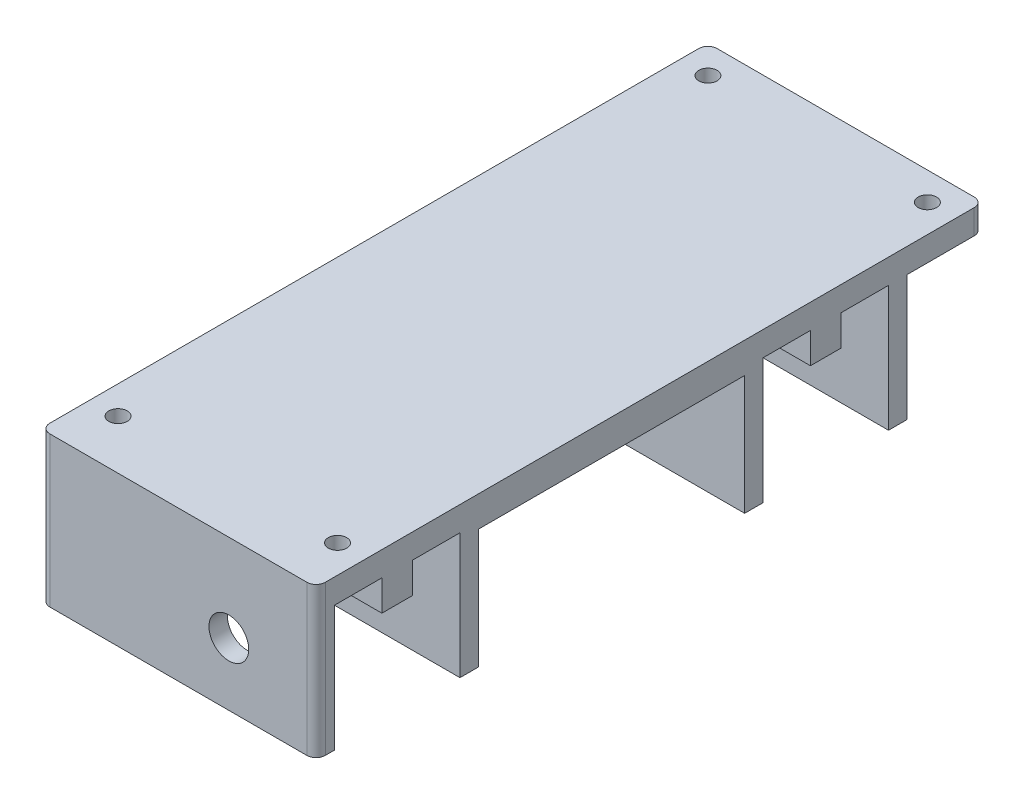
SolidWorks part; units mm, degrees
ref_plane "Front Plane" through (0, 0, 0) normal (0, 0, 1) x (1, 0, 0)
ref_plane "Top Plane" through (0, 0, 0) normal (0, 1, 0) x (1, 0, 0)
ref_plane "Right Plane" through (0, 0, 0) normal (1, 0, 0) x (0, 0, -1)
sketch "Sketch1" plane through (0, 0, 0) normal (0, 1, 0) x (1, 0, 0)
  line L1 (21, -54.5) -> (-21, -54.5)
  line L2 (22.5, -53) -> (22.5, 53)
  line L3 (21, 54.5) -> (-21, 54.5)
  line L4 (-22.5, -53) -> (-22.5, 53)
  line L5 (22.5, -54.5) -> (-22.5, 54.5) construction
  line L6 (22.5, 54.5) -> (-22.5, -54.5) construction
  circle A0 centre (17.925, -46.425) radius 1.5
  circle A1 centre (-17.925, -46.425) radius 1.5
  circle A2 centre (17.925, 49.925) radius 1.5
  circle A3 centre (-17.925, 49.925) radius 1.5
  arc A4 (22.5, 53) -> (21, 54.5) centre (21, 53) ccw
  arc A5 (-21, 54.5) -> (-22.5, 53) centre (-21, 53) ccw
  arc A6 (21, -54.5) -> (22.5, -53) centre (21, -53) ccw
  arc A7 (-21, -54.5) -> (-22.5, -53) centre (-21, -53) cw
  point P0 (0, 0)
  dimension "D3" = 8.075
  dimension "D11" = 1.5
  dimension "D1" = 45
  dimension "D2" = 109
  dimension "D4" = 8.075
  dimension "D5" = 4.575
  dimension "D6" = 4.575
  dimension "D7" = 4.575
  dimension "D8" = 4.575
  dimension "D9" = 4.575
  dimension "D10" = 4.575
extrude "Boss-Extrude1" add sketch "Sketch1" against normal blind 4
sketch "Sketch3" plane through (0, -4, 0) normal (0, -1, 0) x (1, 0, 0)
  line L0 (22.5, 51.5) -> (-22.5, 51.5)
  line L2 (-22.5, 43.75) -> (22.5, 43.75)
  line L3 (-22.5, 43.75) -> (-22.5, 38.75)
  line L4 (22.5, -53) -> (22.5, 53)
  line L5 (21, 54.5) -> (-21, 54.5)
  line L6 (-22.5, 53) -> (-22.5, -53)
  line L7 (-21, -54.5) -> (21, -54.5)
  line L8 (22.5, -53) -> (22.5, 53)
  line L9 (21, 54.5) -> (-21, 54.5)
  line L10 (-22.5, 53) -> (-22.5, -53)
  line L11 (-21, -54.5) -> (21, -54.5)
  line L12 (-22.5, 38.75) -> (22.5, 38.75)
  line L13 (22.5, 43.75) -> (22.5, 38.75)
  line L14 (-22.5, 31) -> (22.5, 31)
  line L15 (-22.5, 31) -> (-22.5, 28)
  line L16 (-22.5, 28) -> (22.5, 28)
  line L17 (22.5, 31) -> (22.5, 28)
  line L18 (-22.5, -15.5) -> (22.5, -15.5)
  line L19 (-22.5, -15.5) -> (-22.5, -18.5)
  line L20 (-22.5, -18.5) -> (22.5, -18.5)
  line L21 (22.5, -15.5) -> (22.5, -18.5)
  line L22 (-22.5, -26.25) -> (22.5, -26.25)
  line L23 (-22.5, -26.25) -> (-22.5, -31.25)
  line L24 (-22.5, -31.25) -> (22.5, -31.25)
  line L25 (22.5, -26.25) -> (22.5, -31.25)
  line L26 (-22.5, -39) -> (22.5, -39)
  line L27 (-22.5, -39) -> (-22.5, -42)
  line L28 (-22.5, -42) -> (22.5, -42)
  line L29 (22.5, -39) -> (22.5, -42)
  arc A4 (21, -54.5) -> (22.5, -53) centre (21, -53) ccw
  arc A5 (22.5, 53) -> (21, 54.5) centre (21, 53) ccw
  arc A6 (-21, 54.5) -> (-22.5, 53) centre (-21, 53) ccw
  arc A7 (-22.5, -53) -> (-21, -54.5) centre (-21, -53) ccw
  arc A8 (21, -54.5) -> (22.5, -53) centre (21, -53) ccw
  arc A9 (22.5, 53) -> (21, 54.5) centre (21, 53) ccw
  arc A10 (-21, 54.5) -> (-22.5, 53) centre (-21, 53) ccw
  arc A11 (-22.5, -53) -> (-21, -54.5) centre (-21, -53) ccw
  line M23 (22.5, -53) -> (22.5, 53)
  arc M24 (22.5, 53) -> (21, 54.5) centre (21, 53) ccw
  line M25 (21, 54.5) -> (-21, 54.5)
  arc M26 (-21, 54.5) -> (-22.5, 53) centre (-21, 53) ccw
  line M27 (-22.5, 53) -> (-22.5, -53)
  dimension "D2" = 3
  dimension "D3" = 7.75
  dimension "D4" = 7.75
  dimension "D5" = 5
  dimension "D6" = 3
  dimension "D7" = 12.5
  dimension "D8" = 3
  dimension "D9" = 5
  dimension "D10" = 3
  dimension "D11" = 7.75
  dimension "D12" = 7.75
  dimension "D1" = 0
extrude "Boss-Extrude2" add sketch "Sketch3" along normal blind 20.5 contours L10 L20 L8 L18 | L10 L24 L8 L22 | L10 L28 L8 L26 | L12 L8 L2 M27 | L0 M23 M24 M25 M26 M27 | L16 L17 L14 L15
sketch "Sketch4" plane through (0, -24.5, 0) normal (0, -1, 0) x (1, 0, 0)
  line L0 (-22.5, 43.75) -> (-22.5, 38.75) construction
  line L1 (-22.5, 38.75) -> (22.5, 38.75) construction
  line L2 (22.5, 38.75) -> (22.5, 43.75) construction
  line L3 (22.5, 43.75) -> (-22.5, 43.75) construction
  line L4 (-22.5, -26.25) -> (-22.5, -31.25) construction
  line L5 (-22.5, -31.25) -> (22.5, -31.25) construction
  line L6 (22.5, -31.25) -> (22.5, -26.25) construction
  line L7 (22.5, -26.25) -> (-22.5, -26.25) construction
  line L8 (-22.5, 43.75) -> (-22.5, 38.75)
  line L9 (-22.5, 38.75) -> (22.5, 38.75)
  line L10 (22.5, 38.75) -> (22.5, 43.75)
  line L11 (22.5, 43.75) -> (-22.5, 43.75)
  line L12 (-22.5, -26.25) -> (-22.5, -31.25)
  line L13 (-22.5, -31.25) -> (22.5, -31.25)
  line L14 (22.5, -31.25) -> (22.5, -26.25)
  line L15 (22.5, -26.25) -> (-22.5, -26.25)
extrude "Cut-Extrude1" cut sketch "Sketch4" against normal blind 15.5
sketch "Sketch5" plane through (0, -4, 0) normal (0, -1, 0) x (1, 0, 0)
  line L4 (22.5, 28) -> (-22.5, 28)
  line L5 (-22.5, 28) -> (-22.5, -15.5)
  line L6 (-22.5, -15.5) -> (22.5, -15.5)
  line L7 (22.5, -15.5) -> (22.5, 28)
  line L8 (22.5, 28) -> (-22.5, 28)
  line L9 (-22.5, 28) -> (-22.5, -15.5)
  line L10 (-22.5, -15.5) -> (22.5, -15.5)
  line L11 (22.5, -15.5) -> (22.5, 28)
  dimension "D1" = 0
extrude "Boss-Extrude3" add sketch "Sketch5" along normal blind 1
sketch "Sketch6" plane through (0, 0, 54.5) normal (0, 0, 1) x (1, 0, 0)
  line L0 (21, -24.5) -> (-21, -24.5) construction
  line L1 (-22.5, -24.5) -> (-22.5, 0) construction
  circle A0 centre (8.25, -14.25) radius 3.25
  dimension "D1" = 10.25
  dimension "D2" = 30.75
extrude "Cut-Extrude2" cut sketch "Sketch6" against normal blind 103 contours A0
sketch "Sketch7" plane through (0, -24.5, 0) normal (0, -1, 0) x (1, 0, 0)
  line L4 (-22.5, 31) -> (-22.5, 28)
  line L5 (-22.5, 28) -> (22.5, 28)
  line L6 (22.5, 28) -> (22.5, 31)
  line L7 (22.5, 31) -> (-22.5, 31)
  line L8 (-22.5, 31) -> (-22.5, 28)
  line L9 (-22.5, 28) -> (22.5, 28)
  line L10 (22.5, 28) -> (22.5, 31)
  line L11 (22.5, 31) -> (-22.5, 31)
  line L12 (-22.5, -15.5) -> (-22.5, -18.5)
  line L13 (-22.5, -18.5) -> (22.5, -18.5)
  line L14 (22.5, -18.5) -> (22.5, -15.5)
  line L15 (22.5, -15.5) -> (-22.5, -15.5)
  line L16 (-22.5, -15.5) -> (-22.5, -18.5)
  line L17 (-22.5, -18.5) -> (22.5, -18.5)
  line L18 (22.5, -18.5) -> (22.5, -15.5)
  line L19 (22.5, -15.5) -> (-22.5, -15.5)
  dimension "D1" = 0
  dimension "D2" = 0
extrude "Boss-Extrude4" add sketch "Sketch7" against normal up to surface (24.5 mm away) up to face at (-17.925, 0, -48.425)
